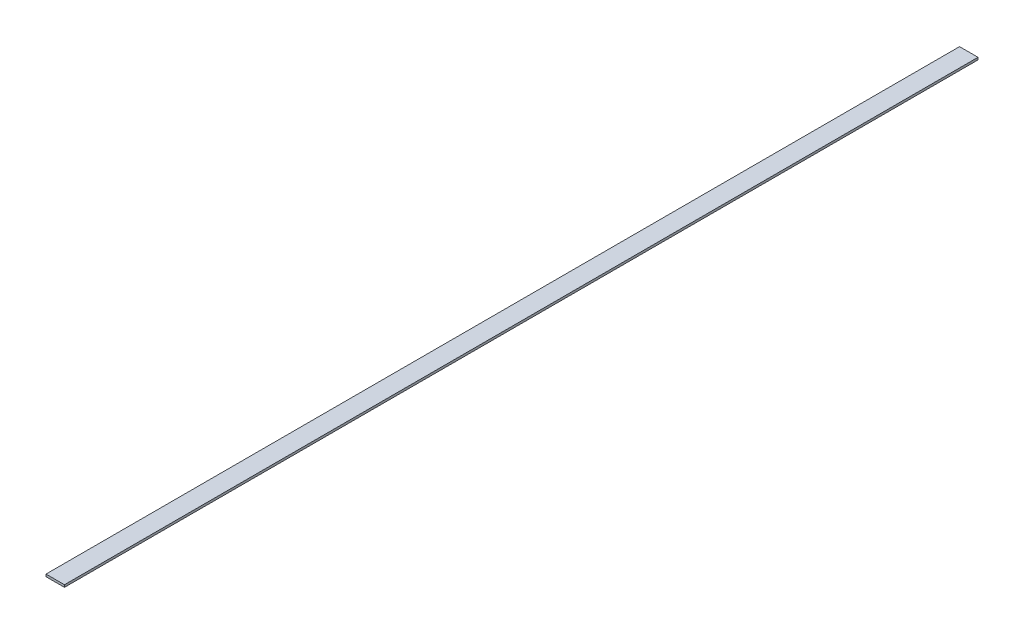
SolidWorks part; units mm, degrees
ref_plane "Plan de face" through (0, 0, 0) normal (0, 0, 1) x (1, 0, 0)
ref_plane "Plan de dessus" through (0, 0, 0) normal (0, 1, 0) x (1, 0, 0)
ref_plane "Plan de droite" through (0, 0, 0) normal (1, 0, 0) x (0, 0, -1)
sketch "Esquisse1" plane through (0, 0, 0) normal (0, 0, 1) x (1, 0, 0)
  line L1 (0, 0) -> (40, 0)
  line L2 (0, 0) -> (0, 5)
  line L3 (0, 5) -> (40, 5)
  line L4 (40, 0) -> (40, 5)
  dimension "D1" = 5
  dimension "D2" = 40
extrude "Boss.-Extru.1" add sketch "Esquisse1" along normal blind 1980
